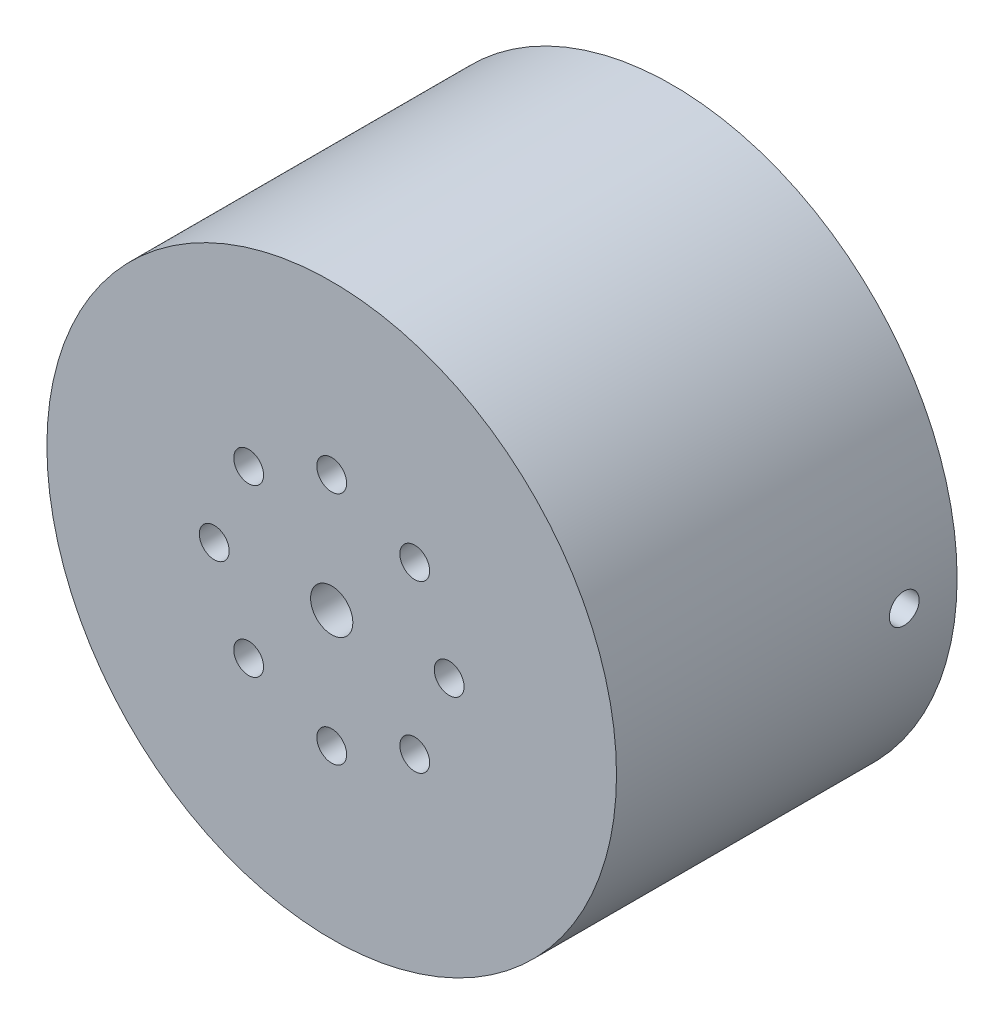
SolidWorks part; units mm, degrees
ref_plane "Front Plane" through (0, 0, 0) normal (0, 0, 1) x (1, 0, 0)
ref_plane "Top Plane" through (0, 0, 0) normal (0, 1, 0) x (1, 0, 0)
ref_plane "Right Plane" through (0, 0, 0) normal (1, 0, 0) x (0, 0, -1)
sketch "Sketch1" plane through (0, 0, 0) normal (0, 0, 1) x (1, 0, 0)
  circle A0 centre (0, 0) radius 14.25
  circle A1 centre (0, 0) radius 24.25
  circle A2 centre (0, 0) radius 4.25
  dimension "D1" = 28.5
  dimension "D2" = 10
  dimension "D3" = 10
extrude "Boss-Extrude1" add sketch "Sketch1" along normal blind 25 contours A1 A0
sketch "Sketch2" plane through (0, 0, 25) normal (0, 0, 1) x (1, 0, 0)
  circle A0 centre (0, 0) radius 1.8
  circle A1 centre (0, 0) radius 24.25
  dimension "D1" = 3.6
extrude "Boss-Extrude2" add sketch "Sketch2" along normal blind 4
sketch "Sketch3" plane through (0, 0, 0) normal (0, 0, -1) x (-1, 0, 0)
  line L1 (-16, -4.445) -> (-21, -4.445)
  line L2 (-16, -4.445) -> (-16, 4.445)
  line L3 (-16, 4.445) -> (-21, 4.445)
  line L4 (-21, -4.445) -> (-21, 4.445)
  line L5 (16, -4.445) -> (21, -4.445)
  line L6 (16, -4.445) -> (16, 4.445)
  line L7 (16, 4.445) -> (21, 4.445)
  line L8 (21, -4.445) -> (21, 4.445)
  point P8 (-16, 0)
  point P10 (16, 0)
  dimension "D1" = 8.89
  dimension "D2" = 8.89
  dimension "D3" = 5
  dimension "D4" = 5
  dimension "D5" = 16
  dimension "D6" = 16
extrude "Cut-Extrude1" cut sketch "Sketch3" against normal blind 11
sketch "Sketch4" plane through (0, 0, 0) normal (1, 0, 0) x (0, 0, -1)
  line L0 (0, -24.25) -> (0, 24.25) construction
  circle A0 centre (-4.5, 0) radius 1.27
  dimension "D1" = 2.54
  dimension "D2" = 4.5
extrude "Cut-Extrude2" cut sketch "Sketch4" against normal mid plane 78
fillet "Fillet1" radius 4 1 edges at (14.25, 0, 25)
sketch "Sketch5" plane through (0, 0, 29) normal (0, 0, 1) x (1, 0, 0)
  circle A0 centre (0, 0) radius 13.352
  circle A1 centre (0, 10) radius 1.27
  circle A2 centre (7.0711, 7.0711) radius 1.27
  circle A3 centre (10, 0) radius 1.27
  circle A4 centre (7.0711, -7.0711) radius 1.27
  circle A5 centre (0, -10) radius 1.27
  circle A6 centre (-7.0711, -7.0711) radius 1.27
  circle A7 centre (-10, 0) radius 1.27
  circle A8 centre (-7.0711, 7.0711) radius 1.27
  point P22 (0, 0)
  dimension "D1" = 10
  dimension "D2" = 2.54
  dimension "D3" = 8
extrude "Cut-Extrude3" cut sketch "Sketch5" against normal blind 78 contours A2 | A8 | A7 | A1 | A6 | A3 | A4 | A5
